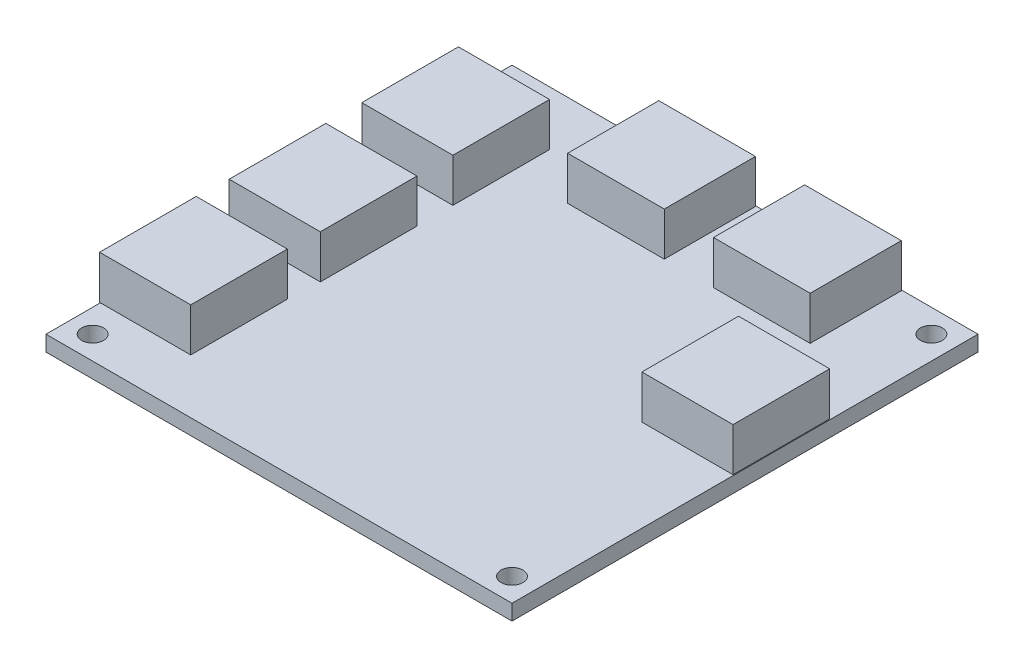
SolidWorks part; units mm, degrees
ref_plane "Front Plane" through (0, 0, 0) normal (0, 0, 1) x (1, 0, 0)
ref_plane "Top Plane" through (0, 0, 0) normal (0, 1, 0) x (1, 0, 0)
ref_plane "Right Plane" through (0, 0, 0) normal (1, 0, 0) x (0, 0, -1)
sketch "Sketch1" plane through (0, 0, 0) normal (0, 1, 0) x (1, 0, 0)
  line L1 (38.1, 38.1) -> (-38.1, 38.1)
  line L2 (38.1, 38.1) -> (38.1, -38.1)
  line L3 (38.1, -38.1) -> (-38.1, -38.1)
  line L4 (-38.1, 38.1) -> (-38.1, -38.1)
  line L5 (38.1, 38.1) -> (-38.1, -38.1) construction
  line L6 (38.1, -38.1) -> (-38.1, 38.1) construction
  point P0 (0, 0)
  dimension "D1" = 76.2
  dimension "D2" = 76.2
extrude "Boss-Extrude1" add sketch "Sketch1" along normal blind 2.54 contours L1 L4 L3 L2
sketch "Sketch2" plane through (0, 2.54, 0) normal (0, 1, 0) x (1, 0, 0)
  line L0 (-38.1, 38.1) -> (-38.1, -38.1) construction
  line L1 (-23.327, -13.41) -> (-38.227, -13.41)
  line L2 (-23.327, -13.41) -> (-23.327, -29.21)
  line L3 (-23.327, -29.21) -> (-38.227, -29.21)
  line L4 (-38.227, -13.41) -> (-38.227, -29.21)
  line L5 (-23.327, -13.41) -> (-38.227, -29.21) construction
  line L6 (-23.327, -29.21) -> (-38.227, -13.41) construction
  line L7 (38.1, -38.1) -> (-38.1, -38.1) construction
  line L12 (-23.073, 29.21) -> (-37.973, 29.21)
  line L13 (-23.073, 29.21) -> (-23.073, 13.41)
  line L14 (-23.073, 13.41) -> (-37.973, 13.41)
  line L15 (-37.973, 29.21) -> (-37.973, 13.41)
  line L20 (38.1, 38.1) -> (-38.1, 38.1) construction
  line L21 (38.1, 38.1) -> (38.1, -38.1) construction
  line L22 (1.83, 23.073) -> (-13.97, 23.073)
  line L23 (1.83, 23.073) -> (1.83, 37.973)
  line L25 (-13.97, 23.073) -> (-13.97, 37.973)
  line L26 (1.83, 23.073) -> (-13.97, 37.973) construction
  line L27 (1.83, 37.973) -> (-13.97, 23.073) construction
  line L28 (9.8818, 37.973) -> (25.6818, 37.973)
  line L29 (9.8818, 37.973) -> (9.8818, 23.073)
  line L30 (9.8818, 23.073) -> (25.6818, 23.073)
  line L31 (25.6818, 37.973) -> (25.6818, 23.073)
  line L32 (9.8818, 37.973) -> (25.6818, 23.073) construction
  line L33 (9.8818, 23.073) -> (25.6818, 37.973) construction
  line L34 (23.073, -1.83) -> (37.973, -1.83)
  line L35 (23.073, -1.83) -> (23.073, 13.97)
  line L36 (23.073, 13.97) -> (37.973, 13.97)
  line L37 (37.973, -1.83) -> (37.973, 13.97)
  line L38 (23.073, -1.83) -> (37.973, 13.97) construction
  line L39 (23.073, 13.97) -> (37.973, -1.83) construction
  line L40 (-13.97, 37.973) -> (1.83, 37.973)
  line L41 (-23.073, -8.2725) -> (-37.973, -8.2725)
  line L42 (-23.073, -8.2725) -> (-23.073, 7.5275)
  line L43 (-23.073, 7.5275) -> (-37.973, 7.5275)
  line L44 (-37.973, -8.2725) -> (-37.973, 7.5275)
  line L45 (-23.073, -8.2725) -> (-37.973, 7.5275) construction
  line L46 (-23.073, 7.5275) -> (-37.973, -8.2725) construction
  point P0 (-30.777, -21.31)
  point P9 (-30.523, -0.3725)
  point P24 (17.7818, 30.523)
  point P30 (30.523, 6.07)
  dimension "D1" = 15.8
  dimension "D2" = 14.9
  dimension "D3" = 0.127
  dimension "D4" = 8.89
  dimension "D5" = 0.127
  dimension "D6" = 0.127
  dimension "D7" = 14.9
  dimension "D8" = 15.8
  dimension "D9" = 0.127
  dimension "D10" = 14.9
  dimension "D11" = 15.8
  dimension "D12" = 8.89
  dimension "D13" = 15.8
  dimension "D14" = 14.9
  dimension "D15" = 24.13
  dimension "D16" = 15.8
  dimension "D17" = 14.9
  dimension "D18" = 0.127
  dimension "D19" = 8.0518
  dimension "D20" = 14.9
  dimension "D21" = 15.8
  dimension "D22" = 0.127
  dimension "D23" = 24.13
extrude "Boss-Extrude2" add sketch "Sketch2" along normal blind 7.1
hole_wizard "9/64 (0.14063) Diameter Hole1" positions "Sketch3" profile "Sketch4" hole size "9/64" standard "ANSI Inch"
sketch "Sketch3" plane through (0, 2.54, 0) normal (0, 1, 0) x (1, 0, 0)
  line L0 (38.1, 38.1) -> (38.1, -38.1) construction
  line L1 (38.1, 38.1) -> (-38.1, 38.1) construction
  line L2 (38.1, 38.1) -> (38.1, -38.1) construction
  line L3 (38.1, -38.1) -> (-38.1, -38.1) construction
  line L4 (-38.1, -29.21) -> (-38.1, -38.1) construction
  line L5 (-38.1, 38.1) -> (-38.1, -13.41) construction
  line L6 (38.1, 38.1) -> (-38.1, 38.1) construction
  point P0 (34.29, -34.29)
  point P2 (-34.29, -34.29)
  point P4 (-34.29, 34.29)
  point P6 (34.29, 34.29)
  dimension "D1" = 3.81
  dimension "D2" = 3.81
  dimension "D3" = 3.81
  dimension "D4" = 3.81
  dimension "D5" = 3.81
  dimension "D6" = 3.81
  dimension "D7" = 3.81
  dimension "D8" = 3.81
sketch "Sketch4" plane through (34.29, 2.54, 34.29) normal (1, 0, 0) x (0, 0, 1)
  line L0 (0, 0) -> (0, 6.8135)
  line L1 (0, 6.8135) -> (1.786, 5.7404)
  line L2 (1.786, 5.7404) -> (1.786, 0)
  line L5 (1.786, 0) -> (0, 0)
  line L10 (0, 6.8135) -> (-1.786, 5.7404) construction
  line L11 (0, -6.35) -> (0, 107.95) construction
  dimension "Hole Dia." = 3.572
  dimension "Hole Depth" = 5.7404
  dimension "Drill Angle" = 118
